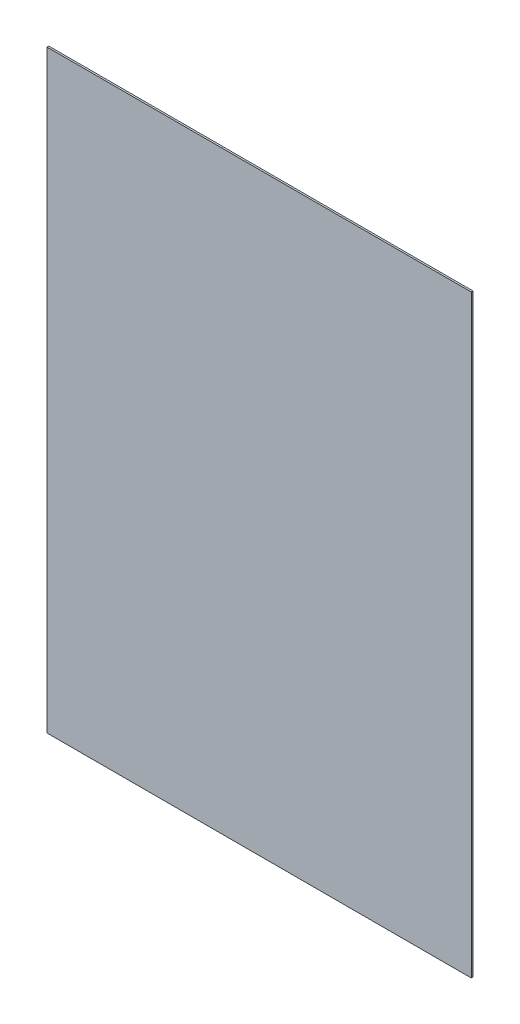
SolidWorks part; units mm, degrees
material "AISI 1020"
ref_plane "Front Plane" through (0, 0, 0) normal (0, 0, 1) x (1, 0, 0)
ref_plane "Top Plane" through (0, 0, 0) normal (0, 1, 0) x (1, 0, 0)
ref_plane "Right Plane" through (0, 0, 0) normal (1, 0, 0) x (0, 0, -1)
sketch "Sketch1" plane through (0, 0, 0) normal (0, 0, 1) x (1, 0, 0)
  line L1 (-381, 533.4) -> (381, 533.4)
  line L2 (-381, 533.4) -> (-381, -533.4)
  line L3 (-381, -533.4) -> (381, -533.4)
  line L4 (381, 533.4) -> (381, -533.4)
  line L5 (-381, 533.4) -> (381, -533.4) construction
  line L6 (-381, -533.4) -> (381, 533.4) construction
  point P0 (0, 0)
  dimension "D1" = 762
  dimension "D2" = 1066.8
extrude "Boss-Extrude1" add sketch "Sketch1" along normal blind 3.175
